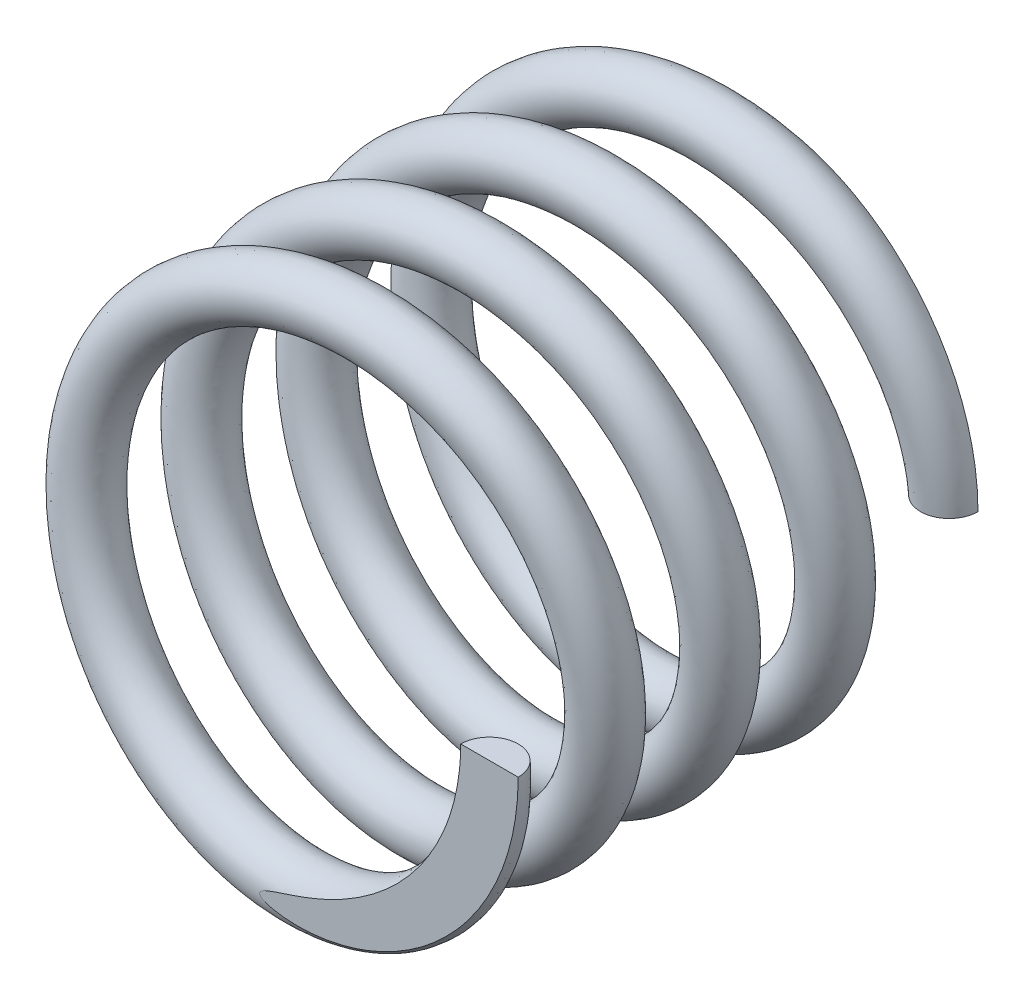
SolidWorks part; units mm, degrees
ref_plane "前视基准面" through (0, 0, 0) normal (0, 0, 1) x (1, 0, 0)
ref_plane "上视基准面" through (0, 0, 0) normal (0, 1, 0) x (1, 0, 0)
ref_plane "右视基准面" through (0, 0, 0) normal (1, 0, 0) x (0, 0, -1)
sketch "草图1" plane through (0, 0, 0) normal (0, 0, 1) x (1, 0, 0)
  circle A0 centre (0, 0) radius 2
  dimension "D1" = 4
curve "螺旋线/涡状线1" pitch 1 height 4 turns 4
sketch "草图2" plane through (0, 0, 0) normal (0, 1, 0) x (1, 0, 0)
  circle A0 centre (2, 0) radius 0.25
  dimension "D1" = 0.5
  dimension "D2" = 2
sweep "扫描1" add profiles "草图2" path "螺旋线/涡状线1"
sketch "草图4" plane through (0, 0, 0) normal (0, 1, 0) x (1, 0, 0)
  line L0 (-2.1087, 0) -> (2.25, 0)
  line L1 (2.25, 0) -> (2.25, -0.4817)
  line L2 (2.25, -0.4817) -> (-2.1087, 0)
  circle A0 centre (2, 0) radius 0.25 construction
extrude "切除-拉伸1" cut sketch "草图4" against normal through all
sketch "草图5" plane through (0, 0, 0) normal (0, -1, 0) x (1, 0, 0)
  line L0 (2.3149, -4.4614) -> (2.3149, -4)
  line L1 (2.3149, -4) -> (-1.6934, -4)
  line L2 (-1.6934, -4) -> (2.3149, -4.4614)
  circle A0 centre (2, -4) radius 0.25 construction
  circle A1 centre (2, -4) radius 0.25 construction
extrude "切除-拉伸2" cut sketch "草图5" against normal blind 10
